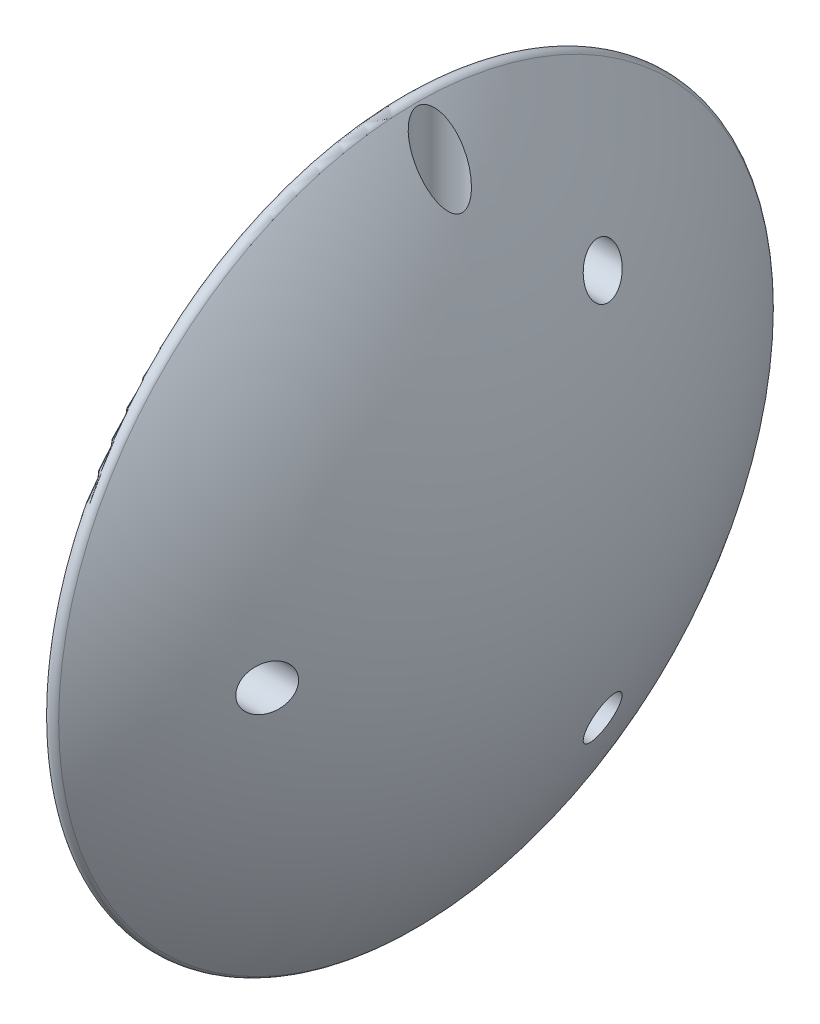
SolidWorks part; units mm, degrees
material "3D_printed_PLA"
ref_plane "Front Plane" through (0, 0, 0) normal (0, 0, 1) x (1, 0, 0)
ref_plane "Top Plane" through (0, 0, 0) normal (0, 1, 0) x (1, 0, 0)
ref_plane "Right Plane" through (0, 0, 0) normal (1, 0, 0) x (0, 0, -1)
sketch "Sketch1" plane through (0, 0, 0) normal (0, 0, 1) x (1, 0, 0)
  line L0 (62.25, 50.2488) -> (62.25, 0)
  line L1 (62.25, 0) -> (80, 0)
  arc A0 (62.25, 50.2488) -> (80, 0) centre (0, 0) cw
  dimension "D1" = 80
  dimension "D2" = 62.25
revolve "Revolve1" add sketch "Sketch1" angle 360 about L1
sketch "Sketch2" plane through (62.25, 0, 0) normal (-1, 0, 0) x (0, 0, 1)
  line L0 (-1.3229, 1.5) -> (1.3229, 1.5)
  arc A0 (-1.3229, 1.5) -> (1.3229, 1.5) centre (0, 0) ccw
  point P4 (0, -2)
  dimension "D1" = 2
  dimension "D2" = 3.5
extrude "Cut-Extrude1" cut sketch "Sketch2" against normal blind 15
sketch "Sketch3" plane through (0, 1.5, 0) normal (0, -1, 0) x (1, 0, 0)
  line L0 (62.25, 1.3229) -> (62.25, -1.3229) construction
  line L1 (77.25, 0) -> (67.25, 0) construction
  line L2 (77.25, 1.3229) -> (77.25, -1.3229) construction
  circle A0 centre (67.25, 0) radius 1.4
  dimension "D2" = 2.8
  dimension "D1" = 5
extrude "Cut-Extrude2" cut sketch "Sketch3" against normal through all
sketch "Sketch4" plane through (0, 1.5, 0) normal (0, -1, 0) x (1, 0, 0)
  circle A0 centre (67.25, 0) radius 3
  dimension "D1" = 6
extrude "Cut-Extrude3" cut sketch "Sketch4" against normal through all from offset 20 offset against normal yes
fillet "Fillet1" radius 1 1 edges at (62.25, 0, 50.2488)
chamfer "Chamfer1" distance 1 angle 45 2 edges at (62.25, 1.5, 0) (62.25, -2, 0)
sketch "Sketch5" plane through (62.25, 0, 0) normal (-1, 0, 0) x (0, 0, 1)
  circle A0 centre (-15, -25.9808) radius 1.4 construction
  circle A1 centre (30, 0) radius 1.4 construction
  circle A2 centre (-15, 25.9808) radius 1.4 construction
  circle A3 centre (-15, -25.9808) radius 1.4
  circle A4 centre (30, 0) radius 1.4
  circle A5 centre (-15, 25.9808) radius 1.4
extrude "Cut-Extrude4" cut sketch "Sketch5" against normal through all both and the other way through all
sketch "Sketch6" plane through (62.25, 0, 0) normal (-1, 0, 0) x (0, 0, 1)
  circle A0 centre (-15, 25.9808) radius 3
  circle A1 centre (30, 0) radius 3
  circle A2 centre (-15, -25.9808) radius 3
  dimension "D1" = 6
extrude "Cut-Extrude5" cut sketch "Sketch6" against normal blind 10 from offset 5
